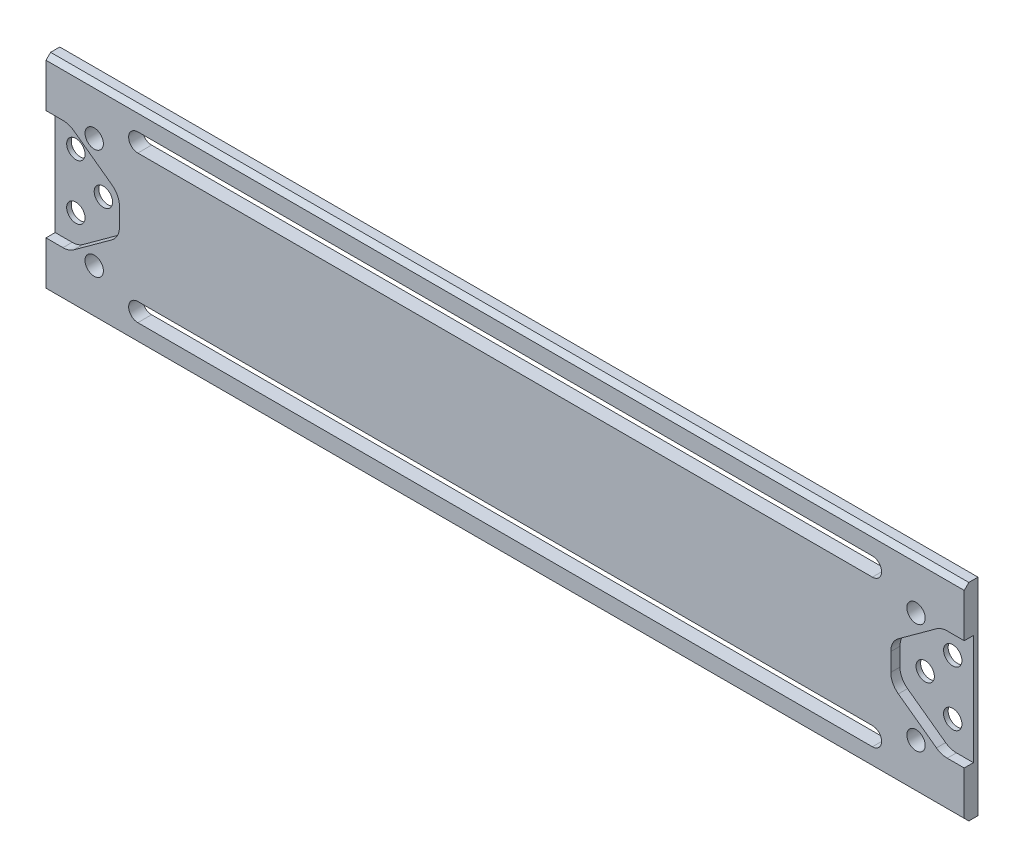
SolidWorks part; units mm, degrees
material "PVC Rigid"
ref_plane "Front Plane" through (0, 0, 0) normal (0, 0, 1) x (1, 0, 0)
ref_plane "Top Plane" through (0, 0, 0) normal (0, 1, 0) x (1, 0, 0)
ref_plane "Right Plane" through (0, 0, 0) normal (1, 0, 0) x (0, 0, -1)
sketch "Sketch1" plane through (0, 0, 0) normal (0, 0, 1) x (1, 0, 0)
  line L1 (-100, 22.5) -> (100, 22.5)
  line L2 (-100, 22.5) -> (-100, -22.5)
  line L3 (-100, -22.5) -> (100, -22.5)
  line L4 (100, 22.5) -> (100, -22.5)
  line L5 (-100, 22.5) -> (100, -22.5) construction
  line L6 (-100, -22.5) -> (100, 22.5) construction
  dimension "D1" = 200
  dimension "D2" = 45
extrude "Boss-Extrude1" add sketch "Sketch1" along normal blind 3
sketch "Sketch2" plane through (0, 0, 0) normal (0, 0, -1) x (-1, 0, 0)
  line L0 (0, 0) -> (100, 0) construction
  line L1 (100, 22.5) -> (100, -22.5) construction
  circle A0 centre (89.5, 0) radius 2
  circle A1 centre (95.5, 6) radius 2
  circle A2 centre (95.5, -6) radius 2
  circle A3 centre (89.5, -12) radius 2
  circle A4 centre (89.5, 12) radius 2
  dimension "D1" = 4
  dimension "D2" = 10.5
  dimension "D3" = 12
  dimension "D4" = 6
  dimension "D5" = 4.5
  dimension "D6" = 12
  dimension "D7" = 12
extrude "Cut-Extrude1" cut sketch "Sketch2" against normal blind 5
ref_plane "Plane1" through (0, 0, 0) normal (1, 0, 0) x (0, 0, -1)
sketch "Sketch3" plane through (0, 0, 3) normal (0, 0, 1) x (1, 0, 0)
  line L0 (0, 0) -> (-10, 0) construction
  line L1 (-10, 0) -> (-10, 14.5) construction
  line L2 (100, 22.5) -> (-100, 22.5) construction
  line L3 (-8, 14.5) -> (-8, 6.5)
  line L5 (-12, 6.5) -> (-12, 14.5)
  arc A0 (-12, 6.5) -> (-8, 6.5) centre (-10, 6.5) ccw
  arc A1 (-8, 14.5) -> (-12, 14.5) centre (-10, 14.5) ccw
  dimension "D1" = 4
  dimension "D2" = 4
  dimension "D3" = 10
  dimension "D4" = 8
  dimension "D5" = 8
ref_plane "Plane3" through (0, 0, 0) normal (0, -1, 0) x (-1, 0, 0)
sketch "Sketch8" plane through (0, 0, 3) normal (0, 0, 1) x (1, 0, 0)
  line L0 (-84, 4) -> (-84, -4)
  line L1 (-84, -4) -> (-95, -12)
  line L2 (-95, -12) -> (-100, -12)
  line L3 (-100, 22.5) -> (-100, -22.5) construction
  line L4 (-84, 4) -> (-95, 12)
  line L5 (-95, 12) -> (-100, 12)
  line L6 (-100, 12) -> (-100, -12)
  line L7 (0, 0) -> (-84, 0) construction
  line L8 (-84, 0) -> (-100, 0) construction
  dimension "D1" = 8
  dimension "D3" = 8
  dimension "D4" = 8
  dimension "D5" = 5
  dimension "D6" = 5
  dimension "D7" = 16
extrude "Cut-Extrude5" cut sketch "Sketch8" against normal blind 2
chamfer "Chamfer2" distance 1 angle 45 2 edges at (0, 22.5, 3) (0, -22.5, 3)
fillet "Fillet1" radius 4 4 edges at (-84, -4, 2) (-84, 4, 2) (-95, 12, 2) (-95, -12, 2)
mirror "Mirror4" about plane through (0, 0, 0) normal (1, 0, 0) of "Fillet1", "Cut-Extrude1", "Cut-Extrude5"
sketch "Sketch9" plane through (0, 0, 3) normal (0, 0, 1) x (1, 0, 0)
  line L0 (80, -18) -> (-80, -18)
  line L1 (0, 0) -> (0, -18) construction
  line L2 (80, -14) -> (-80, -14)
  arc A0 (80, -18) -> (80, -14) centre (80, -16) ccw
  arc A1 (-80, -14) -> (-80, -18) centre (-80, -16) ccw
  point P8 (-71.032, -14)
  dimension "D1" = 4
  dimension "D2" = 18
  dimension "D3" = 80
extrude "Cut-Extrude6" cut sketch "Sketch9" against normal blind 10
mirror "Mirror5" about plane through (0, 0, 0) normal (0, 1, 0) of "Cut-Extrude6"
